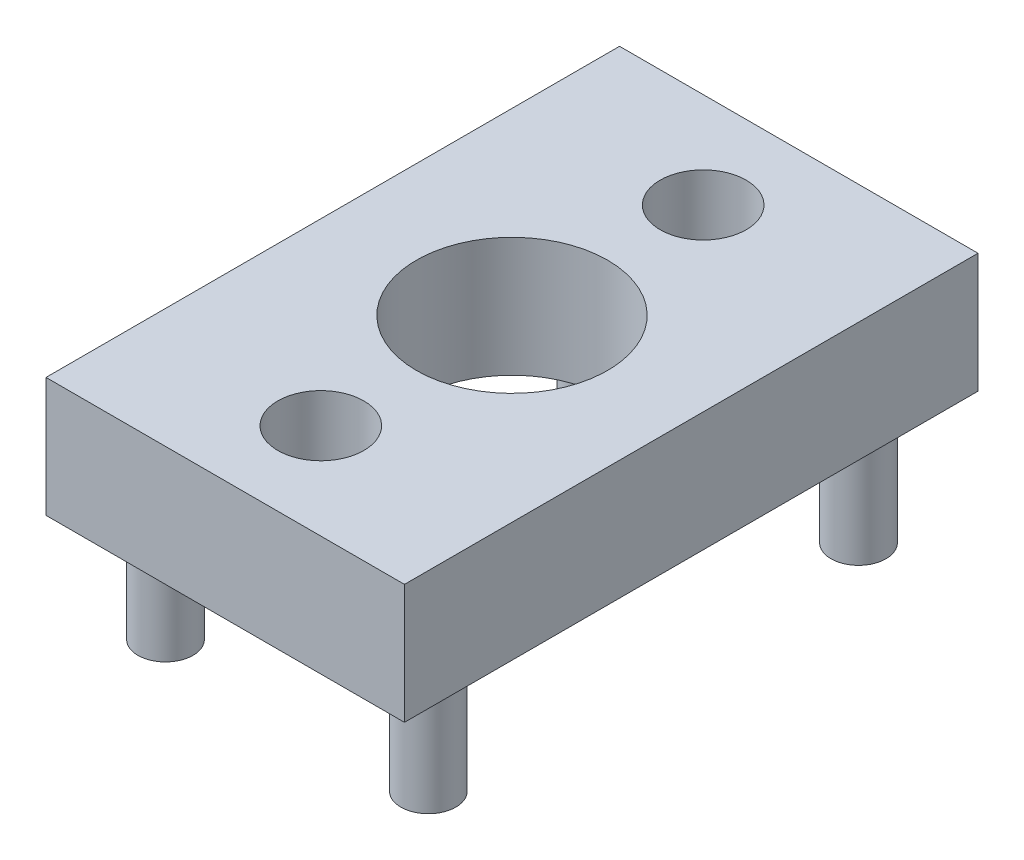
SolidWorks part; units mm, degrees
ref_plane "Front Plane" through (0, 0, 0) normal (0, 0, 1) x (1, 0, 0)
ref_plane "Top Plane" through (0, 0, 0) normal (0, 1, 0) x (1, 0, 0)
ref_plane "Right Plane" through (0, 0, 0) normal (1, 0, 0) x (0, 0, -1)
sketch "Sketch1" plane through (0, 0, 0) normal (1, 0, 0) x (0, 0, -1)
  line L1 (12, -2.5) -> (-12, -2.5)
  line L2 (12, -2.5) -> (12, 2.5)
  line L3 (12, 2.5) -> (-12, 2.5)
  line L4 (-12, -2.5) -> (-12, 2.5)
  line L5 (12, -2.5) -> (-12, 2.5) construction
  line L6 (12, 2.5) -> (-12, -2.5) construction
  point P0 (0, 0)
  dimension "D1" = 24
  dimension "D2" = 5
extrude "Boss-Extrude1" add sketch "Sketch1" along normal blind 15
sketch "Sketch2" plane through (0, -2.5, 0) normal (0, -1, 0) x (1, 0, 0)
  line L0 (2, -9) -> (13, 9) construction
  line L1 (2, 9) -> (13, -9) construction
  circle A0 centre (2, 9) radius 1.15
  circle A1 centre (13, 9) radius 1.15
  circle A2 centre (13, -9) radius 1.15
  circle A3 centre (2, -9) radius 1.15
  point P6 (7.5, 0)
  dimension "D4" = 2.3
  dimension "D1" = 11
  dimension "D2" = 18
  dimension "D3" = 7.5
extrude "Boss-Extrude2" add sketch "Sketch2" along normal blind 5
sketch "Sketch3" plane through (0, 2.5, 0) normal (0, 1, 0) x (1, 0, 0)
  circle A0 centre (7.5, 0) radius 14.1 construction
  dimension "D1" = 28.2
  dimension "D2" = 7.5
sketch "Sketch4" plane through (0, 2.5, 0) normal (0, 1, 0) x (1, 0, 0)
  circle A0 centre (7.5, 0) radius 4
  dimension "D1" = 8
extrude "Cut-Extrude1" cut sketch "Sketch4" against normal through all
sketch "Sketch5" plane through (0, -2.5, 0) normal (0, -1, 0) x (1, 0, 0)
  circle A0 centre (7.5, 0) radius 8 construction
  point P2 (7.5, 8)
  point P4 (7.5, -8)
  dimension "D1" = 16
hole_wizard "CBORE for M3 Pan Head Screw1" positions "Sketch11" profile "Sketch7" counterbore size "M3" standard "ISO" end condition through all
sketch "Sketch11" plane through (0, -2.5, 0) normal (0, -1, 0) x (-1, 0, 0)
  point P0 (-7.5, 8)
  point P3 (-7.5, -8)
sketch "Sketch7" plane through (7.5, -2.5, -8) normal (1, 0, 0) x (0, 0, -1)
  line L0 (0, 0) -> (0, 5)
  line L1 (0, 5) -> (1.8, 5)
  line L3 (1.8, 5) -> (1.8, 2.4)
  line L4 (1.8, 2.4) -> (3.5, 2.4)
  line L5 (3.5, 2.4) -> (3.5, 0)
  line L7 (3.5, 0) -> (0, 0)
  line L11 (0, -6.35) -> (0, 107.95) construction
  dimension "Thru Hole Dia." = 3.6
  dimension "Thru Hole Depth" = 5
  dimension "C'Bore Dia." = 7
  dimension "C'Bore Depth" = 2.4
